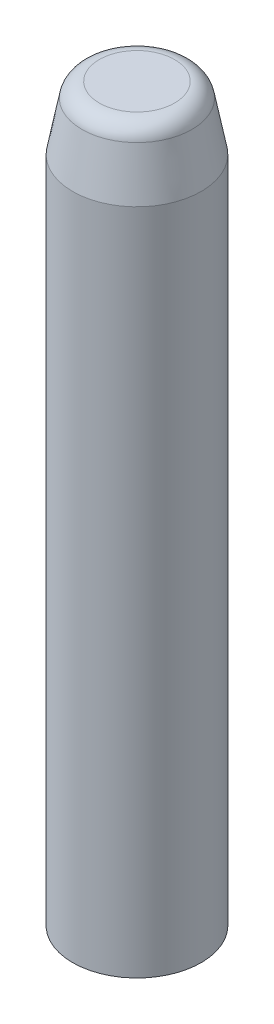
SolidWorks part; units mm, degrees
ref_plane "Front Plane" through (0, 0, 0) normal (0, 0, 1) x (1, 0, 0)
ref_plane "Top Plane" through (0, 0, 0) normal (0, 1, 0) x (1, 0, 0)
ref_plane "Right Plane" through (0, 0, 0) normal (1, 0, 0) x (0, 0, -1)
sketch "Sketch1" plane through (0, 0, 0) normal (0, 1, 0) x (1, 0, 0)
  circle A0 centre (0, 0) radius 6.4
  circle A1 centre (0, 0) radius 3
  dimension "D1" = 12.8
  dimension "D2" = 6
extrude "Boss-Extrude2" add sketch "Sketch1" along normal blind 65
sketch "Sketch2" plane through (0, 0, 0) normal (0, 0, 1) x (1, 0, 0)
  line L0 (-6.4, 65) -> (-6.4, 66.5)
  line L1 (0, 62.5919) -> (0, 74.6709) construction
  line L2 (0, -7.04) -> (0, 7.04) construction
  line L3 (-6.4, 66.5) -> (-5.471, 71.3774)
  line L4 (-3.7519, 72.8) -> (0, 72.8)
  line L5 (3, 65) -> (-3, 65) construction
  line L6 (0, 72.8) -> (0, 65)
  line L7 (0, 65) -> (-6.4, 65)
  arc A0 (-5.471, 71.3774) -> (-3.7519, 72.8) centre (-3.7519, 71.05) cw
  point P3 (-5.2, 72.8)
  point P13 (-5.2, 72.8)
  dimension "D2" = 1.75
  dimension "D4" = 7.8
  dimension "D1" = 1.5
  dimension "D3" = 3.7519
revolve "Revolve2" add sketch "Sketch2" angle 360 about L6
sketch "Sketch4" plane through (0, 0, 0) normal (0, 0, 1) x (1, 0, 0)
  line L0 (0, -7.04) -> (0, 7.04) construction
  circle A0 centre (0, 70) radius 0.5
extrude "Cut-Extrude1" cut sketch "Sketch4" against normal through all
